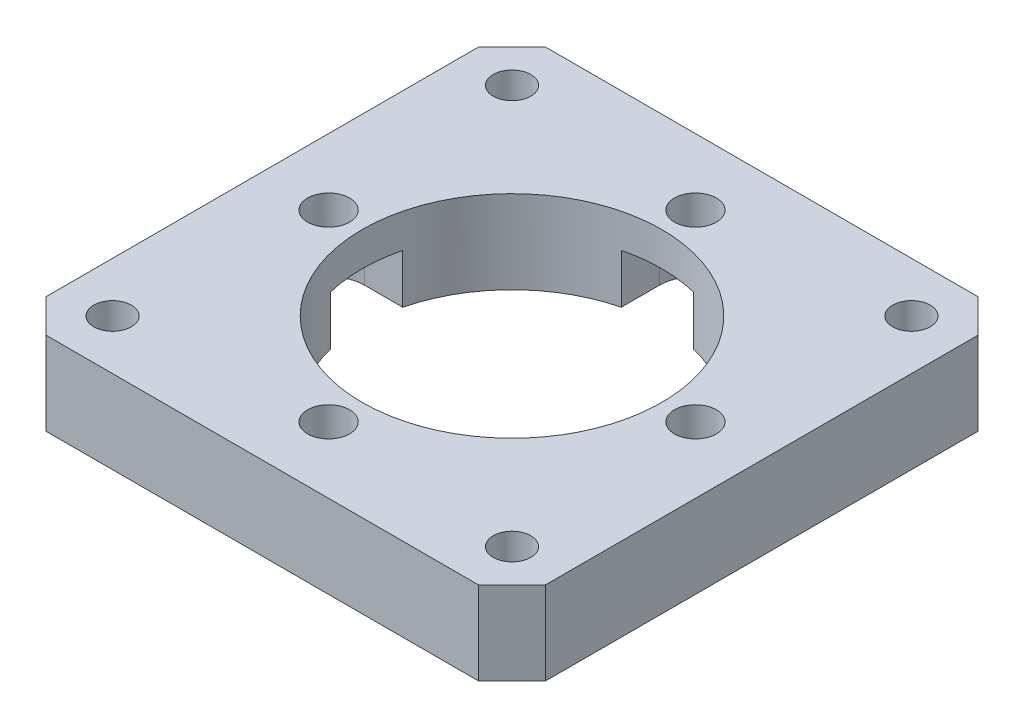
SolidWorks part; units mm, degrees
material "Alum Plate"
ref_plane "Front Plane" through (0, 0, 0) normal (0, 0, 1) x (1, 0, 0)
ref_plane "Top Plane" through (0, 0, 0) normal (0, 1, 0) x (1, 0, 0)
ref_plane "Right Plane" through (0, 0, 0) normal (1, 0, 0) x (0, 0, -1)
other "Bounding Box"
ref_plane "Default Plane" through (0, 2.286, 19.05) normal (0, -1, 0) x (-1, 0, 0)
sketch "Sketch1" plane through (0, 0, 0) normal (0, 1, 0) x (1, 0, 0)
  line L1 (-19.05, 19.05) -> (19.05, 19.05)
  line L2 (-19.05, 19.05) -> (-19.05, -19.05)
  line L3 (-19.05, -19.05) -> (19.05, -19.05)
  line L4 (19.05, 19.05) -> (19.05, -19.05)
  line L5 (-19.05, 19.05) -> (19.05, -19.05) construction
  line L6 (-19.05, -19.05) -> (19.05, 19.05) construction
  circle A0 centre (0, 0) radius 11.43
  point P0 (0, 0)
  dimension "D2" = 22.86
  dimension "D1" = 38.1
extrude "Boss-Extrude1" add sketch "Sketch1" along normal blind 6.35
sketch "Sketch2" plane through (0, 6.35, 0) normal (0, 1, 0) x (1, 0, 0)
  line L0 (0, 0) -> (0, 13.9954) construction
  line L1 (0, 0) -> (15.24, 15.24) construction
  line L2 (15.24, 15.24) -> (19.05, 15.24) construction
  line L3 (19.05, -19.05) -> (19.05, 19.05) construction
  line L4 (15.24, 15.24) -> (15.24, 19.05) construction
  line L5 (19.05, 19.05) -> (-19.05, 19.05) construction
  circle A0 centre (0, 13.9954) radius 1.6002
  circle A1 centre (15.24, 15.24) radius 1.4351
  dimension "D1" = 3.2004
  dimension "D3" = 2.8702
  dimension "D2" = 13.9954
  dimension "D4" = 3.81
extrude "Cut-Extrude1" cut sketch "Sketch2" against normal through all
pattern_circular "CirPattern1" count 4 over 360 about axis through (0, 0, 0) along (0, 1, 0) of "Cut-Extrude1"
chamfer "Chamfer1" distance 2.54 angle 45 4 edges at (-19.05, 3.175, 19.05) (19.05, 3.175, 19.05) (19.05, 3.175, -19.05) (-19.05, 3.175, -19.05)
sketch "Sketch3" plane through (0, 0, 0) normal (0, -1, 0) x (1, 0, 0)
  line L0 (0, 13.9954) -> (0, 0) construction
  line L1 (2.7559, 13.9954) -> (2.7559, 0)
  line L2 (-2.7559, 13.9954) -> (-2.7559, 0)
  arc A0 (2.7559, 13.9954) -> (-2.7559, 13.9954) centre (0, 13.9954) ccw
  arc A1 (-2.7559, 0) -> (2.7559, 0) centre (0, 0) ccw
  point P4 (0, 6.9977)
  dimension "D1" = 2.7559
extrude "Cut-Extrude2" cut sketch "Sketch3" against normal blind 3.7592
pattern_circular "CirPattern4" count 4 over 360 about axis through (0, 0, 0) along (0, 1, 0) of "Cut-Extrude2"
equation "\"Unit Measure\"= \"BoundingVolume\" / \"Thickness\"'in^2"
